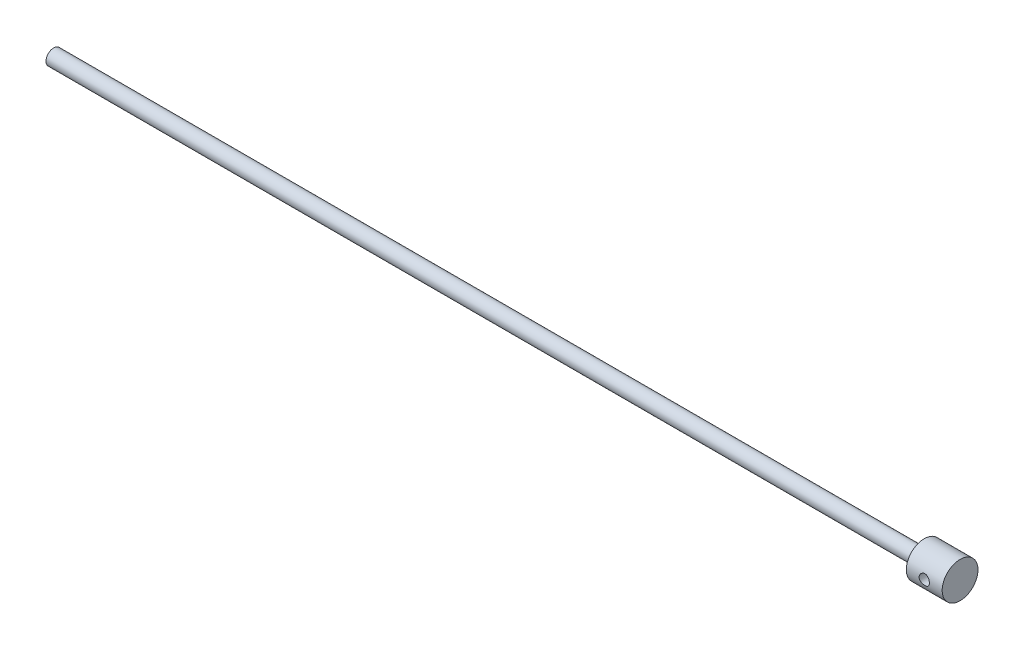
SolidWorks part; units mm, degrees
ref_plane "Front Plane" through (0, 0, 0) normal (0, 0, 1) x (1, 0, 0)
ref_plane "Top Plane" through (0, 0, 0) normal (0, 1, 0) x (1, 0, 0)
ref_plane "Right Plane" through (0, 0, 0) normal (1, 0, 0) x (0, 0, -1)
sketch "Sketch1" plane through (0, 0, 0) normal (1, 0, 0) x (0, 0, -1)
  circle A0 centre (0, 0) radius 7.5
  dimension "D1" = 15
extrude "Boss-Extrude1" add sketch "Sketch1" against normal blind 850
sketch "Sketch2" plane through (0, 0, 0) normal (1, 0, 0) x (0, 0, -1)
  circle A0 centre (0, 0) radius 17.5
  dimension "D1" = 35
extrude "Boss-Extrude2" add sketch "Sketch2" along normal blind 35
sketch "Sketch3" plane through (0, 0, 0) normal (0, 0, 1) x (1, 0, 0)
  circle A0 centre (17.5, 0) radius 5
  dimension "D1" = 10
  dimension "D2" = 17.5
extrude "Cut-Extrude2" cut sketch "Sketch3" against normal through all both and the other way through all contours A0
